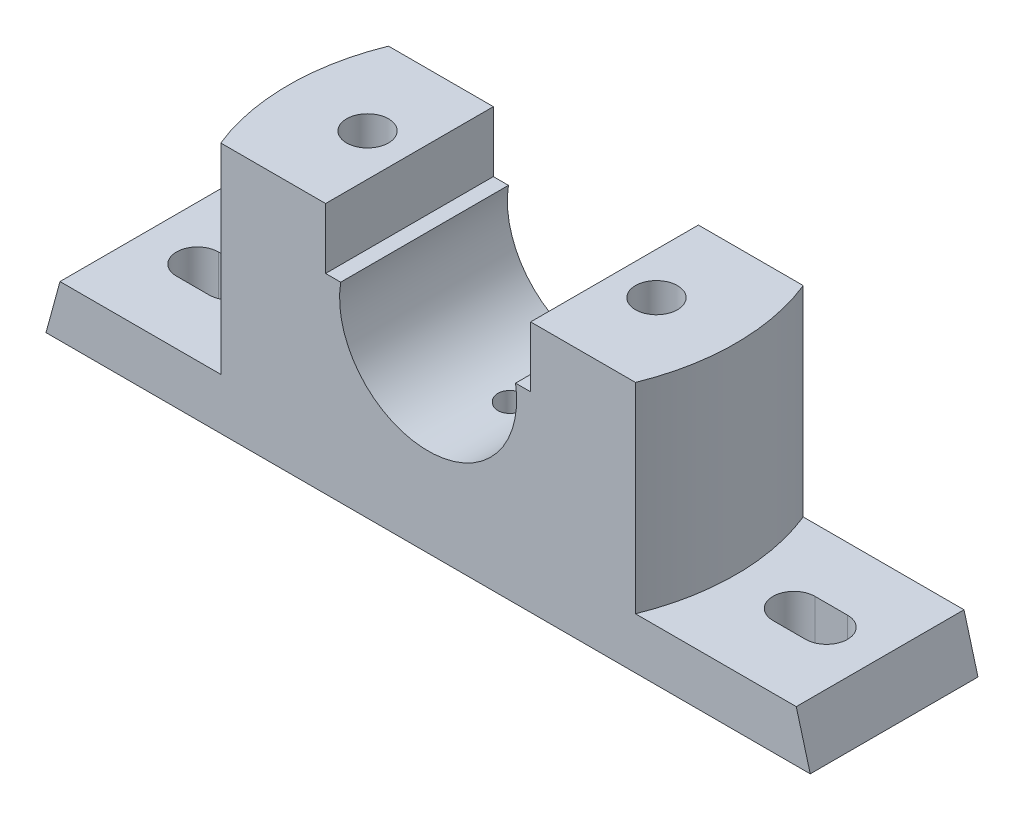
SolidWorks part; units mm, degrees
ref_plane "Front Plane" through (0, 0, 0) normal (0, 0, 1) x (1, 0, 0)
ref_plane "Top Plane" through (0, 0, 0) normal (0, 1, 0) x (1, 0, 0)
ref_plane "Right Plane" through (0, 0, 0) normal (1, 0, 0) x (0, 0, -1)
sketch "Sketch2" plane through (0, 0, 0) normal (0, 0, 1) x (1, 0, 0)
  line L0 (0, -89.9616) -> (0, 89.9616) construction
  line L1 (18.7617, 3) -> (22, 3)
  line L2 (22, 3) -> (22, 16)
  line L3 (22, 16) -> (50, 16)
  line L4 (50, 16) -> (50, -27)
  line L5 (50, -27) -> (79, -27)
  line L6 (79, -27) -> (82, -38)
  line L7 (82, -38) -> (-82, -38)
  line L8 (-79, -27) -> (-82, -38)
  line L9 (-50, -27) -> (-79, -27)
  line L10 (-50, 16) -> (-50, -27)
  line L11 (-22, 16) -> (-50, 16)
  line L12 (-22, 3) -> (-22, 16)
  line L13 (-18.7617, 3) -> (-22, 3)
  arc A0 (-18.7617, 3) -> (18.7617, 3) centre (0, 0) ccw
  point P4 (0, 0)
  point P16 (0, -38)
  dimension "D1" = 19
  dimension "D2" = 164
  dimension "D3" = 16
  dimension "D4" = 13
  dimension "D5" = 44
  dimension "D6" = 54
  dimension "D7" = 11
  dimension "D8" = 3
  dimension "D9" = 50
extrude "Boss-Extrude1" add sketch "Sketch2" along normal mid plane 36
hole_wizard "Ø1.0mm Dowel Hole3" positions "Sketch11" profile "Sketch10" hole size "Ø1.0" standard "ANSI Metric" end condition through all
sketch "Sketch11" plane through (0, 16, 0) normal (0, 1, 0) x (1, 0, 0)
  line L0 (0, 0) -> (0, 54.1379) construction
  point P0 (-31, 0)
  point P2 (31, 0)
  dimension "D1" = 62
sketch "Sketch10" plane through (-31, 16, 0) normal (1, 0, 0) x (0, 0, 1)
  line L0 (0, 0) -> (0, 54)
  line L1 (0, 54) -> (4.5, 54)
  line L2 (4.5, 54) -> (4.5, 0)
  line L5 (4.5, 0) -> (0, 0)
  line L11 (0, -6.35) -> (0, 107.95) construction
  dimension "Thru Hole Dia." = 9
  dimension "Thru Hole Depth" = 54
sketch "Sketch12" plane through (0, -38, 0) normal (0, -1, 0) x (1, 0, 0)
  line L1 (-21, -10) -> (-41, -10)
  line L2 (-21, -10) -> (-21, 10)
  line L3 (-21, 10) -> (-41, 10)
  line L4 (-41, -10) -> (-41, 10)
  line L5 (-21, -10) -> (-41, 10) construction
  line L6 (-21, 10) -> (-41, -10) construction
  point P0 (-31, 0)
  dimension "D1" = 20
  dimension "D2" = 20
extrude "Cut-Extrude2" cut sketch "Sketch12" against normal blind 6
sketch "Sketch13" plane through (0, -27, 0) normal (0, 1, 0) x (1, 0, 0)
  line L0 (-67.5, 0) -> (-60.5, 0) construction
  line L1 (-67.5, 4.5) -> (-60.5, 4.5)
  line L2 (-67.5, -4.5) -> (-60.5, -4.5)
  line L3 (0, -71.2416) -> (0, 71.2416) construction
  line L4 (60.5, 0) -> (67.5, 0) construction
  line L5 (60.5, 4.5) -> (67.5, 4.5)
  line L6 (60.5, -4.5) -> (67.5, -4.5)
  arc A0 (-67.5, 4.5) -> (-67.5, -4.5) centre (-67.5, 0) ccw
  arc A1 (-60.5, -4.5) -> (-60.5, 4.5) centre (-60.5, 0) ccw
  circle A2 centre (-64, 0) radius 4.5 construction
  arc A3 (60.5, 4.5) -> (60.5, -4.5) centre (60.5, 0) ccw
  arc A4 (67.5, -4.5) -> (67.5, 4.5) centre (67.5, 0) ccw
  circle A5 centre (64, 0) radius 4.5 construction
  point P2 (-64, 0)
  point P13 (0, 0)
  point P15 (64, 0)
  dimension "D3" = 9
  dimension "D1" = 9
  dimension "D5" = 9
  dimension "D2" = 16
  dimension "D4" = 16
  dimension "D6" = 128
extrude "Cut-Extrude3" cut sketch "Sketch13" against normal through all
mirror "Mirror1" about plane through (0, 0, 0) normal (1, 0, 0) of "Cut-Extrude2"
sketch "Sketch17" plane through (0, 16, 0) normal (0, 1, 0) x (1, 0, 0)
  line L0 (-22, 18) -> (-50, 18) construction
  line L1 (-50, -18) -> (-50, 18) construction
  line L2 (-22, -18) -> (-50, -18) construction
  line L3 (-44.4972, 18) -> (-50, 18)
  line L4 (-50, -18) -> (-50, 18)
  line L5 (-44.4972, -18) -> (-50, -18)
  arc A0 (-44.4972, 18) -> (-44.4972, -18) centre (0, 0) ccw
  dimension "D1" = 48
extrude "Cut-Extrude4" cut sketch "Sketch17" against normal blind 43
mirror "Mirror3" about plane through (0, 0, 0) normal (1, 0, 0) of "Cut-Extrude4"
hole_wizard "Ø1.0mm Dowel Hole4" positions "3DSketch1" profile "Sketch19" hole size "Ø1.0" standard "ANSI Metric"
sketch3d "3DSketch1"
  point P0 (0, -19, 0)
  dimension "D1" = 0
  dimension "D2" = 0
sketch "Sketch19" plane through (0, -19, 0) normal (1, 0, 0) x (0, 0, 1)
  line L0 (0, 0) -> (0, 7.8026)
  line L1 (0, 7.8026) -> (3, 6)
  line L2 (3, 6) -> (3, 0)
  line L5 (3, 0) -> (0, 0)
  line L10 (0, 7.8026) -> (-3, 6) construction
  line L11 (0, -6.35) -> (0, 107.95) construction
  dimension "Hole Dia." = 6
  dimension "Hole Depth" = 6
  dimension "Drill Angle" = 118
